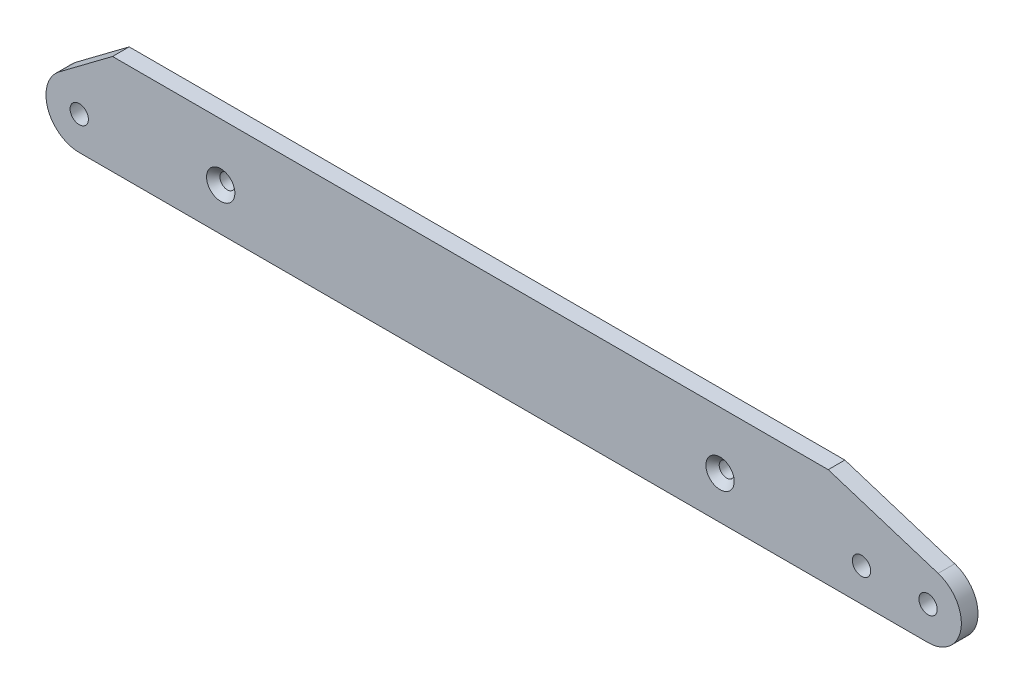
SolidWorks part; units mm, degrees
material "ABS"
ref_plane "Front Plane" through (0, 0, 0) normal (0, 0, 1) x (1, 0, 0)
ref_plane "Top Plane" through (0, 0, 0) normal (0, 1, 0) x (1, 0, 0)
ref_plane "Right Plane" through (0, 0, 0) normal (1, 0, 0) x (0, 0, -1)
sketch "Sketch1" plane through (0, 0, 0) normal (0, 0, 1) x (1, 0, 0)
  line L1 (-117.5, -12.8) -> (137.5, -12.8)
  line L5 (107.5, 17.2) -> (-107.5, 17.2)
  line L6 (-107.5, 17.2) -> (-123.5, 5.2)
  line L7 (107.5, 17.2) -> (140.5217, 6.7325)
  line L8 (-107.5, 17.2) -> (-107.5, -12.8) construction
  line L9 (-75, 0) -> (75, 0) construction
  line L10 (107.5, 17.2) -> (107.5, -12.8) construction
  line L11 (-107.5, 0) -> (-75, 0) construction
  line L12 (75, 0) -> (107.5, 0) construction
  line L13 (-127.5, -2.8) -> (-117.5, -2.8) construction
  line L15 (-117.5, -2.8) -> (-107.5, -2.8) construction
  line L16 (147.5, -2.8) -> (137.5, -2.8) construction
  line L17 (137.5, -2.8) -> (117.5, -2.8) construction
  line L18 (117.5, -2.8) -> (107.5, -2.8) construction
  circle A0 centre (75, 0) radius 2.25
  circle A1 centre (-75, 0) radius 2.25
  circle A2 centre (-117.5, -2.8) radius 2.75
  circle A4 centre (117.5, -2.8) radius 2.75
  circle A5 centre (137.5, -2.8) radius 2.75
  arc A7 (-123.5, 5.2) -> (-117.5, -12.8) centre (-117.5, -2.8) ccw
  arc A8 (137.5, -12.8) -> (140.5217, 6.7325) centre (137.5, -2.8) ccw
  point P1 (-141.3834, 9.5051)
  point P3 (0, 0)
  point P26 (0, 0)
  point P28 (0, 0)
  point P30 (0, 0)
  point P31 (-119.9924, -2.8)
  point P32 (153.4315, -2.8)
  point P33 (0, 0)
  dimension "D2" = 150
  dimension "D8" = 4.5
  dimension "D10" = 5.5
  dimension "D1" = 30
  dimension "D3" = 32.5
  dimension "D4" = 215
  dimension "D5" = 10
  dimension "D6" = 20
  dimension "D7" = 12.8
extrude "Boss-Extrude1" add sketch "Sketch1" along normal mid plane 5
chamfer "Chamfer1" distance 2 angle 45 2 edges at (77.25, 0, 2.5) (-72.75, 0, 2.5)
